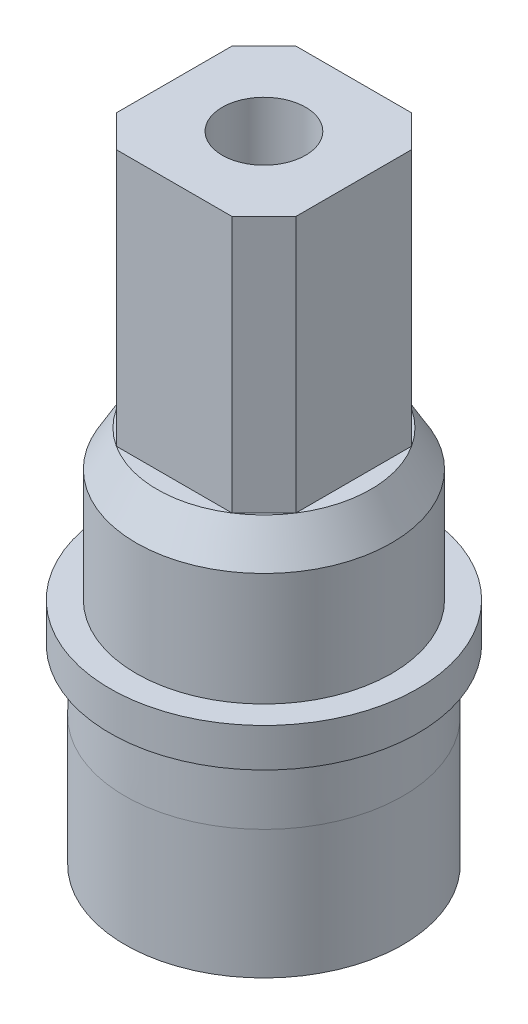
SolidWorks part; units mm, degrees
ref_plane "Front Plane" through (0, 0, 0) normal (0, 0, 1) x (1, 0, 0)
ref_plane "Top Plane" through (0, 0, 0) normal (0, 1, 0) x (1, 0, 0)
ref_plane "Right Plane" through (0, 0, 0) normal (1, 0, 0) x (0, 0, -1)
sketch "Sketch1" plane through (0, 0, 0) normal (0, 0, 1) x (1, 0, 0)
  line L0 (0, 0) -> (0, 12.6983) construction
  line L1 (-2.7, 0) -> (-2.7, 5.54)
  line L2 (-2.7, 5.54) -> (-1.295, 5.54)
  line L3 (-1.295, 5.54) -> (-1.295, 8.3)
  line L4 (-1.295, 8.3) -> (-3.32, 8.3)
  line L5 (-3.32, 8.3) -> (-3.97, 7.1844)
  line L6 (-3.97, 7.1844) -> (-3.97, 3.67)
  line L7 (-3.97, 3.67) -> (-4.785, 3.67)
  line L8 (-4.785, 3.67) -> (-4.785, 2.47)
  line L9 (-4.785, 2.47) -> (-4.28, 2.47)
  line L10 (-4.28, 2.47) -> (-4.325, 0)
  line L11 (-4.325, 0) -> (-2.7, 0)
  dimension "D1" = 9.57
  dimension "D2" = 8.3
  dimension "D3" = 3.67
  dimension "D4" = 1.2
  dimension "D5" = 8.65
  dimension "D6" = 8.56
  dimension "D7" = 5.4
  dimension "D8" = 6.64
  dimension "D9" = 7.94
  dimension "D10" = 1.1156
  dimension "D11" = 2.59
  dimension "D12" = 5.54
revolve "Revolve1" add sketch "Sketch1" angle 360 about L0
sketch "Sketch2" plane through (0, 8.3, 0) normal (0, 1, 0) x (1, 0, 0)
  line L0 (1.7995, 2.79) -> (-1.7995, 2.79)
  line L1 (-1.7995, 2.79) -> (-2.79, 1.7995)
  line L2 (-2.79, 1.7995) -> (-2.79, -1.7995)
  line L3 (-2.79, -1.7995) -> (-1.7995, -2.79)
  line L4 (-1.7995, -2.79) -> (1.7995, -2.79)
  line L5 (1.7995, -2.79) -> (2.79, -1.7995)
  line L6 (2.79, -1.7995) -> (2.79, 1.7995)
  line L7 (2.79, 1.7995) -> (1.7995, 2.79)
  circle A0 centre (0, 0) radius 3.32 construction
  circle A1 centre (0, 0) radius 1.295
  dimension "D1" = 5.58
  dimension "D2" = 1.4007
extrude "Boss-Extrude1" add sketch "Sketch2" along normal blind 7.7
sketch "Sketch3" plane through (0, 5.54, 0) normal (0, -1, 0) x (1, 0, 0)
  circle A0 centre (0, 0) radius 2.7
extrude "Boss-Extrude4" add sketch "Sketch3" along normal blind 6
sketch "Sketch5" plane through (0, -0.46, 0) normal (0, -1, 0) x (1, 0, 0)
  circle A0 centre (0, 0) radius 4.4845
extrude "Cut-Extrude1" cut sketch "Sketch5" against normal blind 1
sketch "Sketch6" plane through (0, 0.54, 0) normal (0, -1, 0) x (1, 0, 0)
  circle A0 centre (0, 0) radius 4.3152
  circle A1 centre (0, 0) radius 4.3152
  dimension "D1" = 8.6303
sketch "Sketch8" plane through (0, 0.54, 0) normal (0, -1, 0) x (1, 0, 0)
  circle A1 centre (0, 0) radius 4.315
  dimension "D2" = 8.63
  dimension "D1" = 0
extrude "Boss-Extrude8" add sketch "Sketch8" along normal blind 8 separate body
sketch "Sketch13" plane through (0, -7.46, 0) normal (0, -1, 0) x (1, 0, 0)
  line L0 (-0.9654, -1.2759) -> (1.1452, -1.1173)
  circle A0 centre (0, 0) radius 1.6
  dimension "D1" = 3.2
  dimension "D2" = 1.6
  dimension "D3" = 1.6
  dimension "D4" = 1.2
extrude "Cut-Extrude4" cut sketch "Sketch13" against normal blind 10.2 contours L0 A0
sketch "Sketch14" plane through (-2.79, 0, 0) normal (-1, 0, 0) x (0, 0, 1)
  line L0 (1.7995, 10.9798) -> (-1.7995, 10.9798)
  line L1 (1.7995, 16) -> (1.7995, 8.3) construction
  line L2 (-1.7995, 16) -> (-1.7995, 8.3) construction
  line L3 (-1.7995, 11.4054) -> (-1.7995, 16)
  line L4 (-1.7995, 16) -> (1.7995, 16)
  line L5 (1.7995, 16) -> (1.7995, 10.9798)
  line L6 (-1.7995, 10.9798) -> (-1.7995, 11.4054)
  line L8 (4.4221, 16) -> (-3.9947, 16)
  line L9 (4.4221, 16) -> (4.4221, 11.2829)
  line L10 (4.4221, 11.2829) -> (-3.9947, 11.2829)
  line L11 (-3.9947, 16) -> (-3.9947, 11.2829)
  line L12 (4.4221, 16) -> (-3.9947, 11.2829) construction
  line L13 (4.4221, 11.2829) -> (-3.9947, 16) construction
  point P9 (0.2137, 13.6415)
  line M4 (1.7995, 16) -> (-1.7995, 16)
  line M5 (-1.7995, 16) -> (-1.7995, 8.3)
  dimension "D1" = 0
extrude "Cut-Extrude11" cut sketch "Sketch14" against normal through all both and the other way through all contours L10 L5 M4 M5 | L10 L9 L8 L5 | L8 L11 L10 M5
ref_plane "Plane1" through (2.79, 11.2829, 1.7995) normal (0, -1, 0) x (-1, 0, 0)
sketch "Sketch16" plane through (0, 11.2829, 0) normal (0, 1, 0) x (1, 0, 0)
  line L0 (-2.79, -1.7995) -> (-2.79, 1.7995)
  line L1 (-2.79, 1.7995) -> (-1.7995, 2.79)
  line L2 (-1.7995, 2.79) -> (1.7995, 2.79)
  line L3 (1.7995, 2.79) -> (2.79, 1.7995)
  line L4 (2.79, 1.7995) -> (2.79, -1.7995)
  line L5 (2.79, -1.7995) -> (1.7995, -2.79)
  line L6 (1.7995, -2.79) -> (-1.7995, -2.79)
  line L7 (-1.7995, -2.79) -> (-2.79, -1.7995)
  circle A0 centre (0, 0) radius 1.295
extrude "Boss-Extrude9" add sketch "Sketch16" along normal blind 5
sketch "Sketch21" plane through (0, -7.46, 0) normal (0, -1, 0) x (1, 0, 0)
  line L0 (-0.9654, -1.2759) -> (1.1452, -1.1173)
  circle A0 centre (0, 0) radius 1.6
  line M1 (1.1452, -1.1173) -> (-0.9654, -1.2759)
  arc M2 (-0.9654, -1.2759) -> (1.1452, -1.1173) centre (0, 0) cw
extrude "Cut-Extrude12" cut sketch "Sketch21" against normal blind 14 contours M1 M2
sketch "Sketch22" plane through (0, -7.46, 0) normal (0, -1, 0) x (1, 0, 0)
  line L0 (1.1452, -1.1173) -> (-0.9654, -1.2759)
  circle A0 centre (0, 0) radius 4.315
  circle A1 centre (0, 0) radius 1.6
  line M1 (1.1452, -1.1173) -> (-0.9654, -1.2759)
  arc M2 (-0.9654, -1.2759) -> (1.1452, -1.1173) centre (0, 0) cw
  circle M3 centre (0, 0) radius 4.315
extrude "Cut-Extrude14" cut sketch "Sketch22" against normal blind 4 contours A1 M3 M2 | A1 M1
